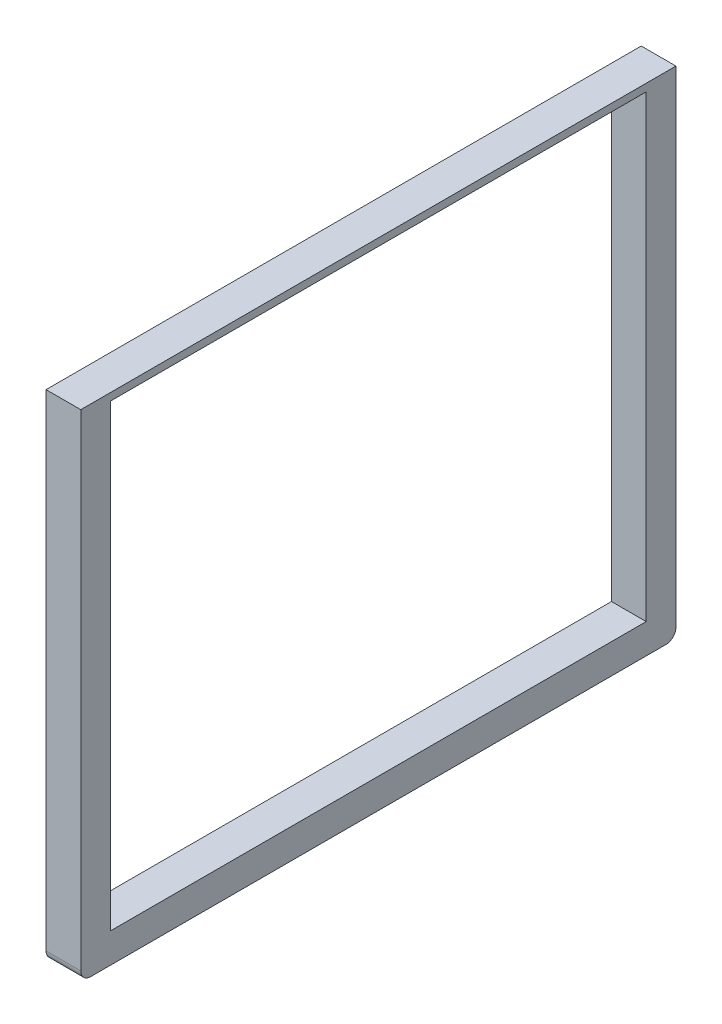
SolidWorks part; units mm, degrees
ref_plane "Front Plane" through (0, 0, 0) normal (0, 0, 1) x (1, 0, 0)
ref_plane "Top Plane" through (0, 0, 0) normal (0, 1, 0) x (1, 0, 0)
ref_plane "Right Plane" through (0, 0, 0) normal (1, 0, 0) x (0, 0, -1)
sketch "Sketch1" plane through (0, 0, 0) normal (1, 0, 0) x (0, 0, -1)
  line L1 (-310.4982, 250) -> (289.5015, 250)
  line L2 (-310.4982, 250) -> (-310.4982, -250)
  line L3 (-310.4982, -250) -> (289.5018, -250)
  line L4 (289.5015, 250) -> (289.5018, -250)
  line L5 (-310.4982, 250) -> (289.5018, -250) construction
  line L6 (-310.4982, -250) -> (289.5015, 250) construction
  point P0 (0, 0)
  point P5 (289.5018, 250)
  dimension "D1" = 500
  dimension "D2" = 500
  dimension "D3" = 600
extrude "Boss-Extrude1" add sketch "Sketch1" along normal blind 35
sketch "Sketch2" plane through (35, 0, 0) normal (1, 0, 0) x (0, 0, -1)
  line L0 (289.5015, 250) -> (-310.4982, 250) construction
  line L3 (-280.4982, 242.5) -> (259.5015, 242.5)
  line L4 (289.5018, -250) -> (289.5015, 250) construction
  line L5 (-310.4982, 250) -> (-310.4982, -250) construction
  line L6 (-280.4982, 242.5) -> (-280.4982, -220)
  line L7 (-280.4982, -220) -> (259.5015, -220)
  line L8 (259.5015, -220) -> (259.5015, 242.5)
  line L9 (-310.4982, -250) -> (289.5018, -250) construction
  dimension "D1" = 7.5
  dimension "D2" = 30
  dimension "D3" = 30
  dimension "D4" = 30
extrude "Cut-Extrude1" cut sketch "Sketch2" against normal blind 35
fillet "Fillet1" radius 10 2 edges at (17.5, -250, -289.5018) (17.5, -250, 310.4982)
